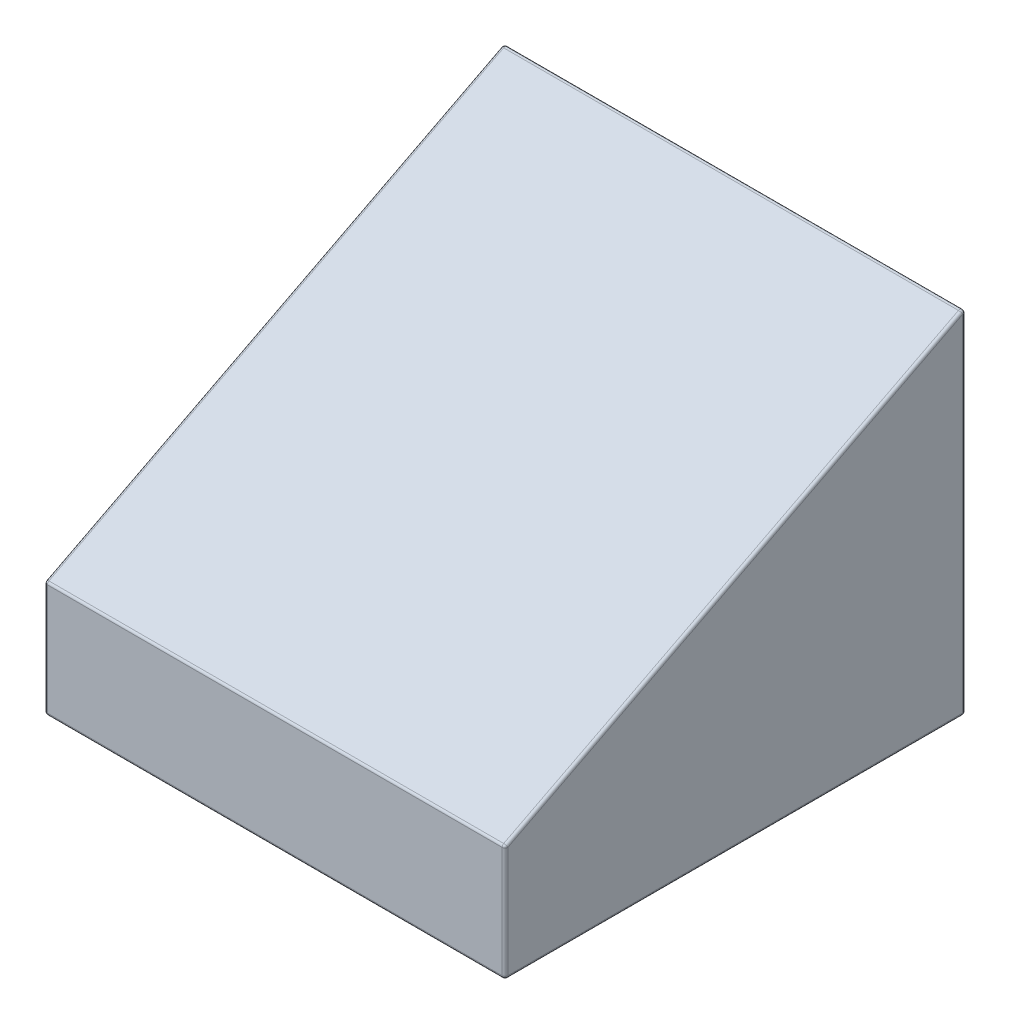
SolidWorks part; units mm, degrees
material "Smoked Clear Plastic"
ref_plane "Front Plane" through (0, 0, 0) normal (0, 0, 1) x (1, 0, 0)
ref_plane "Top Plane" through (0, 0, 0) normal (0, 1, 0) x (1, 0, 0)
ref_plane "Right Plane" through (0, 0, 0) normal (1, 0, 0) x (0, 0, -1)
sketch "Sketch1" plane through (0, 0, 0) normal (0, 1, 0) x (1, 0, 0)
  line L1 (-3.98, 3.98) -> (3.98, 3.98)
  line L2 (-3.98, 3.98) -> (-3.98, -3.98)
  line L3 (-3.98, -3.98) -> (3.98, -3.98)
  line L4 (3.98, 3.98) -> (3.98, -3.98)
  line L5 (-3.98, 3.98) -> (3.98, -3.98) construction
  line L6 (-3.98, -3.98) -> (3.98, 3.98) construction
  point P0 (0, 0)
  dimension "D1" = 7.96
extrude "Extrude1" add sketch "Sketch1" along normal blind 6.3
sketch "Sketch2" plane through (3.98, 0, 0) normal (1, 0, 0) x (0, 0, -1)
  line L0 (-3.98, 2.2) -> (3.98, 6.3)
  line L1 (-3.98, 6.3) -> (-3.98, 0) construction
  line L2 (3.98, 6.3) -> (-3.98, 6.3)
  line L3 (-3.98, 6.3) -> (-3.98, 2.2)
  dimension "D1" = 2.2
extrude "Extrude2" cut sketch "Sketch2" against normal through all
shell "Shell1" thickness 1.55
sketch "Sketch5" plane through (-2.43, 0, 0) normal (1, 0, 0) x (0, 0, -1)
  line L0 (-2.43, 0) -> (2.43, 0) construction
  line L3 (-2.43, 0) -> (2.43, 0)
  line L4 (2.43, 0) -> (2.43, 3.9156)
  line L5 (-2.43, 0) -> (-2.43, 1.4123)
  line L6 (2.43, 3.9156) -> (-2.43, 1.4123)
  line L7 (-2.43, 1.2548) -> (2.43, 3.7581) construction
  dimension "D1" = 0.14
extrude "Extrude4" cut sketch "Sketch5" along normal up to surface (4.86 mm away) up to face at (2.43, 1.2532, 0)
sketch "Sketch6" plane through (0, 0, 0) normal (0, -1, 0) x (1, 0, 0)
  line L0 (-3.98, 3.98) -> (3.98, 3.98) construction
  line L1 (3.98, 3.98) -> (3.98, -3.98) construction
  line L2 (3.98, -3.98) -> (-3.98, -3.98) construction
  line L3 (-3.98, -3.98) -> (-3.98, 3.98) construction
  line L4 (-3.98, 3.98) -> (3.98, 3.98)
  line L5 (3.98, 3.98) -> (3.98, -3.98)
  line L6 (3.98, -3.98) -> (-3.98, -3.98)
  line L7 (-3.98, -3.98) -> (-3.98, 3.98)
  line L8 (-3.78, 3.78) -> (3.78, 3.78)
  line L9 (3.78, 3.78) -> (3.78, -3.78)
  line L10 (3.78, -3.78) -> (-3.78, -3.78)
  line L11 (-3.78, -3.78) -> (-3.78, 3.78)
  dimension "D1" = 0.2
extrude "Extrude5" cut sketch "Sketch6" against normal blind 0.2
fillet "Fillet1" radius 0.05 36 edges at (-3.78, 0, 0) (0, 0, -3.78) (3.78, 0, 0) (0, 0, 3.78) (-3.78, 0.2, 0) (0, 0.2, -3.78) (3.78, 0.2, 0) (0, 0.2, 3.78) (-3.78, 0.1, -3.78) (3.78, 0.1, -3.78) (3.78, 0.1, 3.78) (-3.78, 0.1, 3.78) (-3.98, 0.2, 0) (0, 0.2, -3.98) (3.98, 0.2, 0) (0, 0.2, 3.98) (-2.43, 2.664, 0) (2.43, 2.664, 0) (0, 1.4123, 2.43) (0, 3.9156, -2.43) (2.43, 0, 0) (0, 0, -2.43) (-2.43, 0, 0) (0, 0, 2.43) (2.43, 0.7062, 2.43) (-2.43, 0.7062, 2.43) (-2.43, 1.9578, -2.43) (2.43, 1.9578, -2.43) (3.98, 4.25, 0) (-3.98, 4.25, 0) (0, 2.2, 3.98) (0, 6.3, -3.98) (3.98, 1.2, 3.98) (-3.98, 1.2, 3.98) (-3.98, 3.25, -3.98) (3.98, 3.25, -3.98)
